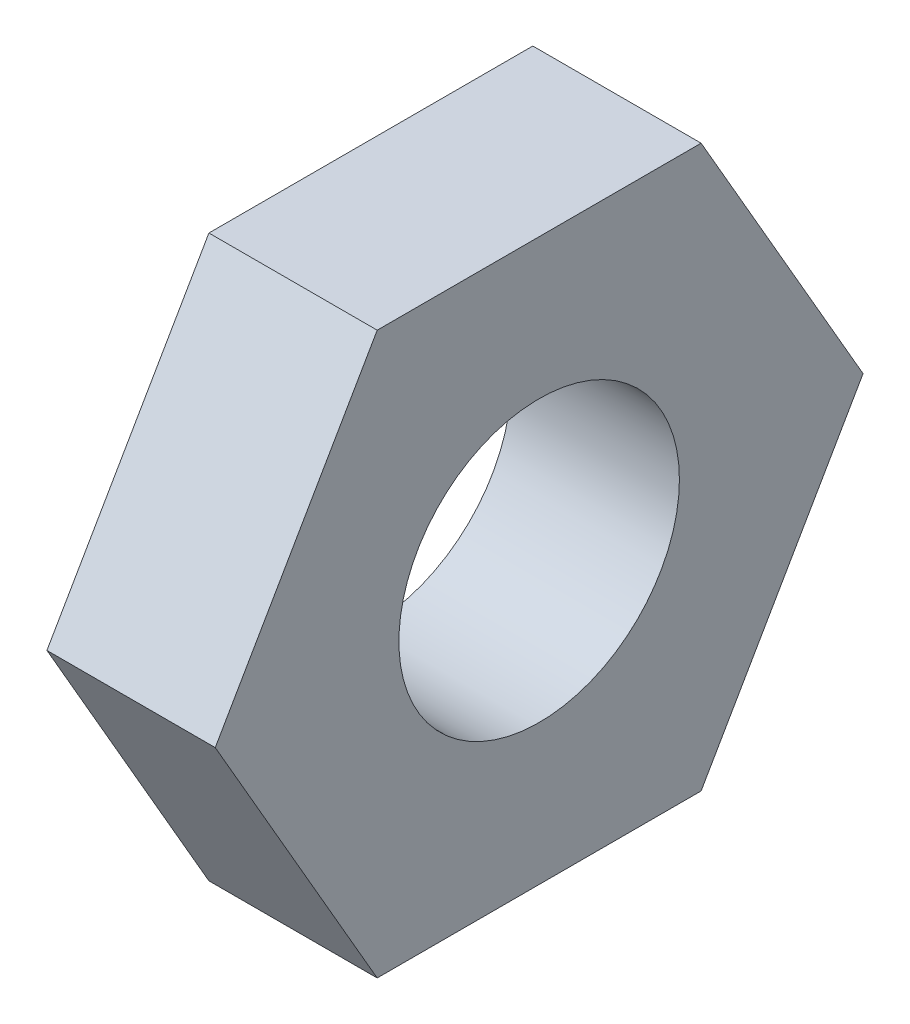
SolidWorks part; units mm, degrees
ref_plane "Front Plane" through (0, 0, 0) normal (0, 0, 1) x (1, 0, 0)
ref_plane "Top Plane" through (0, 0, 0) normal (0, 1, 0) x (1, 0, 0)
ref_plane "Right Plane" through (0, 0, 0) normal (1, 0, 0) x (0, 0, -1)
sketch "Sketch1" plane through (0, 0, 0) normal (1, 0, 0) x (0, 0, -1)
  line L1 (5.7735, 0) -> (2.8868, 5)
  line L2 (2.8868, 5) -> (-2.8868, 5)
  line L3 (-2.8868, 5) -> (-5.7735, 0)
  line L4 (-5.7735, 0) -> (-2.8868, -5)
  line L5 (-2.8868, -5) -> (2.8868, -5)
  line L6 (2.8868, -5) -> (5.7735, 0)
  circle A0 centre (0, 0) radius 5 construction
  circle A1 centre (0, 0) radius 2.5
  dimension "D1" = 10
  dimension "D2" = 5
extrude "Boss-Extrude1" add sketch "Sketch1" along normal blind 3
